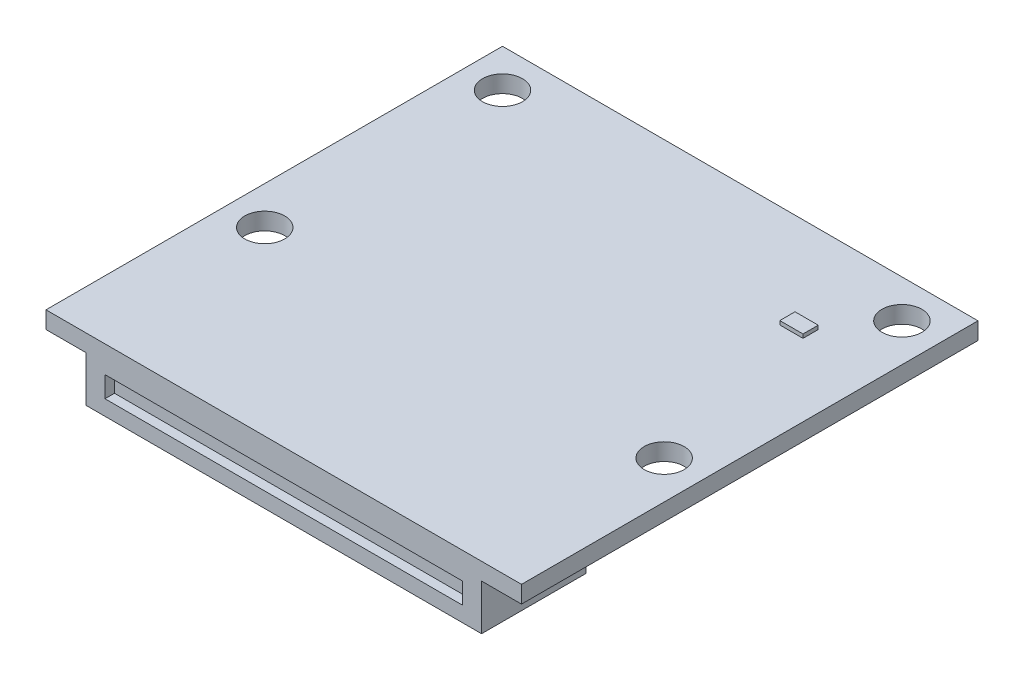
SolidWorks part; units mm, degrees
material "Epoxid, Ungefüllt"
ref_plane "Vorne" through (0, 0, 0) normal (0, 0, 1) x (1, 0, 0)
ref_plane "Oben" through (0, 0, 0) normal (0, 1, 0) x (1, 0, 0)
ref_plane "Rechts" through (0, 0, 0) normal (1, 0, 0) x (0, 0, -1)
sketch "Skizze1" plane through (0, 0, 0) normal (0, 1, 0) x (1, 0, 0)
  line L0 (0, 14.5) -> (0, -9.5) construction
  line L1 (-12.5, 14.5) -> (12.5, 14.5)
  line L2 (-12.5, 14.5) -> (-12.5, -9.5)
  line L3 (-12.5, -9.5) -> (12.5, -9.5)
  line L4 (12.5, 14.5) -> (12.5, -9.5)
  dimension "D1" = 24
  dimension "D2" = 25
  dimension "D3" = 9.5
extrude "PCB" add sketch "Skizze1" against normal blind 0.9
sketch "Skizze2" plane through (0, 0, 0) normal (0, 1, 0) x (1, 0, 0)
  line L0 (12.5, 14.5) -> (-12.5, 14.5) construction
  line L1 (12.5, -9.5) -> (12.5, 14.5) construction
  line L2 (0, 0) -> (0, 9.3158) construction
  circle A0 centre (10.5, 12.5) radius 1.05
  circle A1 centre (10.5, 0) radius 1.05
  circle A2 centre (-10.5, 0) radius 1.05
  circle A3 centre (-10.5, 12.5) radius 1.05
  dimension "D1" = 2.1
  dimension "D2" = 2
  dimension "D3" = 2
  dimension "D4" = 12.5
extrude "Mounting_Holes" cut sketch "Skizze2" against normal through all
sketch "Skizze3" plane through (0, -0.9, 0) normal (0, -1, 0) x (1, 0, 0)
  line L0 (0, 4) -> (0, 0) construction
  line L1 (-10.4, 9.5) -> (10.4, 9.5)
  line L2 (-10.4, 9.5) -> (-10.4, 4)
  line L3 (-10.4, 4) -> (10.4, 4)
  line L4 (10.4, 9.5) -> (10.4, 4)
  line L5 (-12.5, 9.5) -> (12.5, 9.5) construction
  dimension "D1" = 20.8
  dimension "D2" = 5.5
extrude "Connector_closed" add sketch "Skizze3" along normal blind 2.4
sketch "Esquisse1" plane through (0, 0, 0) normal (0, 1, 0) x (1, 0, 0)
  line L0 (12.5, 14.5) -> (-12.5, 14.5) construction
  line L1 (8.7, 9.1) -> (7.48, 9.1)
  line L2 (8.7, 9.1) -> (8.7, 9.9)
  line L3 (8.7, 9.9) -> (7.48, 9.9)
  line L4 (7.48, 9.1) -> (7.48, 9.9)
  line L5 (12.5, -9.5) -> (12.5, 14.5) construction
  dimension "D1" = 1.22
  dimension "D2" = 0.8
  dimension "D3" = 4.6
  dimension "D4" = 3.8
extrude "Status LED" add sketch "Esquisse1" along normal blind 0.2
sketch "Esquisse3" plane through (0, 0, 9.5) normal (0, 0, 1) x (1, 0, 0)
  line L0 (-10.4, -3.3) -> (-10.4, -0.9) construction
  line L1 (-9.4, -1.4) -> (9.4, -1.4)
  line L2 (-9.4, -1.4) -> (-9.4, -2.5)
  line L3 (-9.4, -2.5) -> (9.4, -2.5)
  line L4 (9.4, -1.4) -> (9.4, -2.5)
  line L5 (10.4, -3.3) -> (10.4, -0.9) construction
  line L6 (10.4, -3.3) -> (-10.4, -3.3) construction
  line L7 (-12.5, 0) -> (12.5, 0) construction
  dimension "D1" = 1
  dimension "D2" = 1
  dimension "D3" = 0.8
  dimension "D4" = 1.4
extrude "Enlèv. mat.-Extru.1" cut sketch "Esquisse3" against normal blind 0.5
